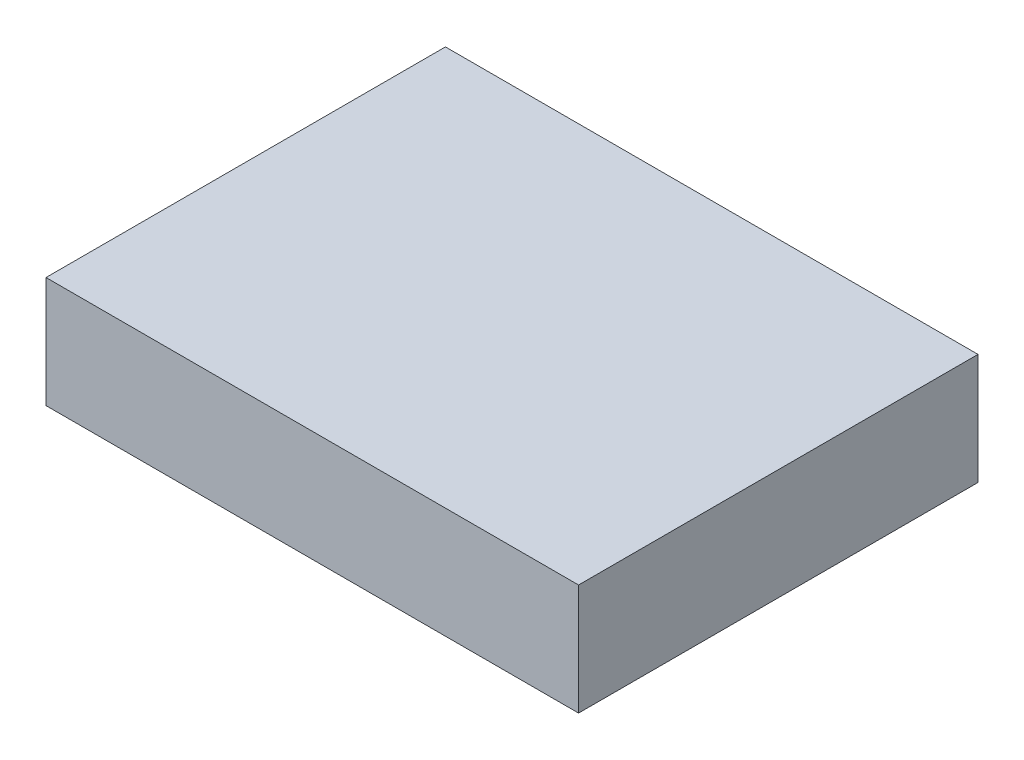
SolidWorks part; units mm, degrees
ref_plane "Front Plane" through (0, 0, 0) normal (0, 0, 1) x (1, 0, 0)
ref_plane "Top Plane" through (0, 0, 0) normal (0, 1, 0) x (1, 0, 0)
ref_plane "Right Plane" through (0, 0, 0) normal (1, 0, 0) x (0, 0, -1)
sketch "Sketch1" plane through (0, 0, 0) normal (0, 1, 0) x (1, 0, 0)
  line L1 (-12, -9) -> (12, -9)
  line L2 (-12, -9) -> (-12, 9)
  line L3 (-12, 9) -> (12, 9)
  line L4 (12, -9) -> (12, 9)
  line L5 (0, 9) -> (0, -9) construction
  line L6 (-12, 0) -> (12, 0) construction
  point P0 (0, 0)
  dimension "D1" = 24
  dimension "D2" = 18
extrude "Boss-Extrude1" add sketch "Sketch1" along normal blind 5
